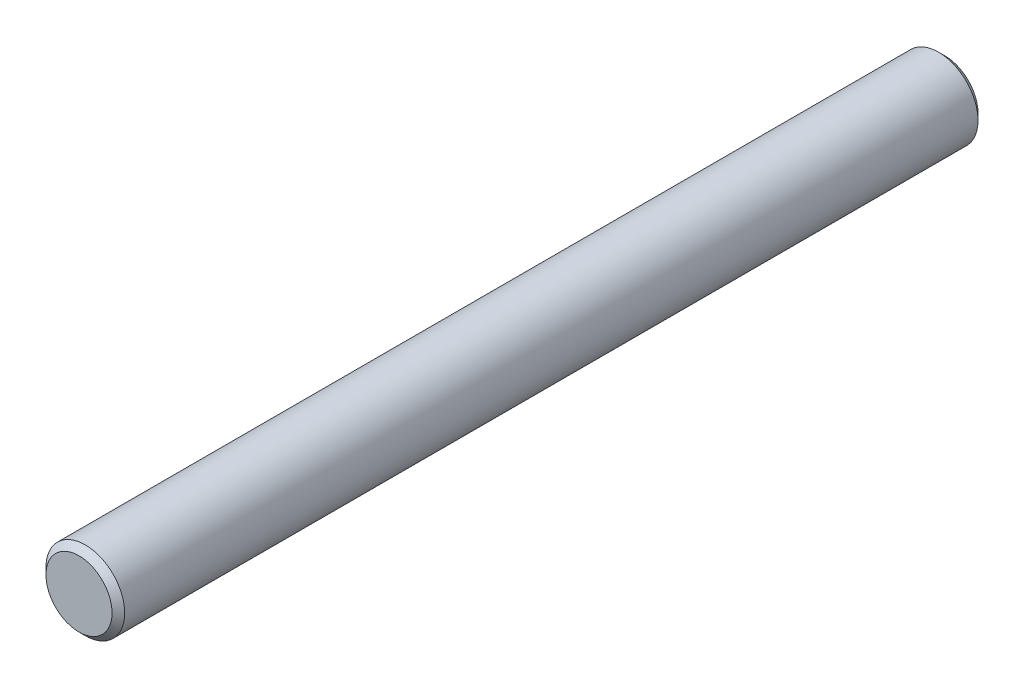
SolidWorks part; units mm, degrees
material "1023 Carbon Steel Sheet (SS)"
ref_plane "Front Plane" through (0, 0, 0) normal (0, 0, 1) x (1, 0, 0)
ref_plane "Top Plane" through (0, 0, 0) normal (0, 1, 0) x (1, 0, 0)
ref_plane "Right Plane" through (0, 0, 0) normal (1, 0, 0) x (0, 0, -1)
sketch "Sketch2" plane through (0, 0, 0) normal (0, 0, 1) x (1, 0, 0)
  circle A0 centre (0, 0) radius 1.25
  dimension "D1" = 2.5
extrude "Boss-Extrude1" add sketch "Sketch2" along normal mid plane 27.5
chamfer "Chamfer1" distance 0.2 angle 45 2 edges at (1.25, 0, -13.75) (1.25, 0, 13.75)
